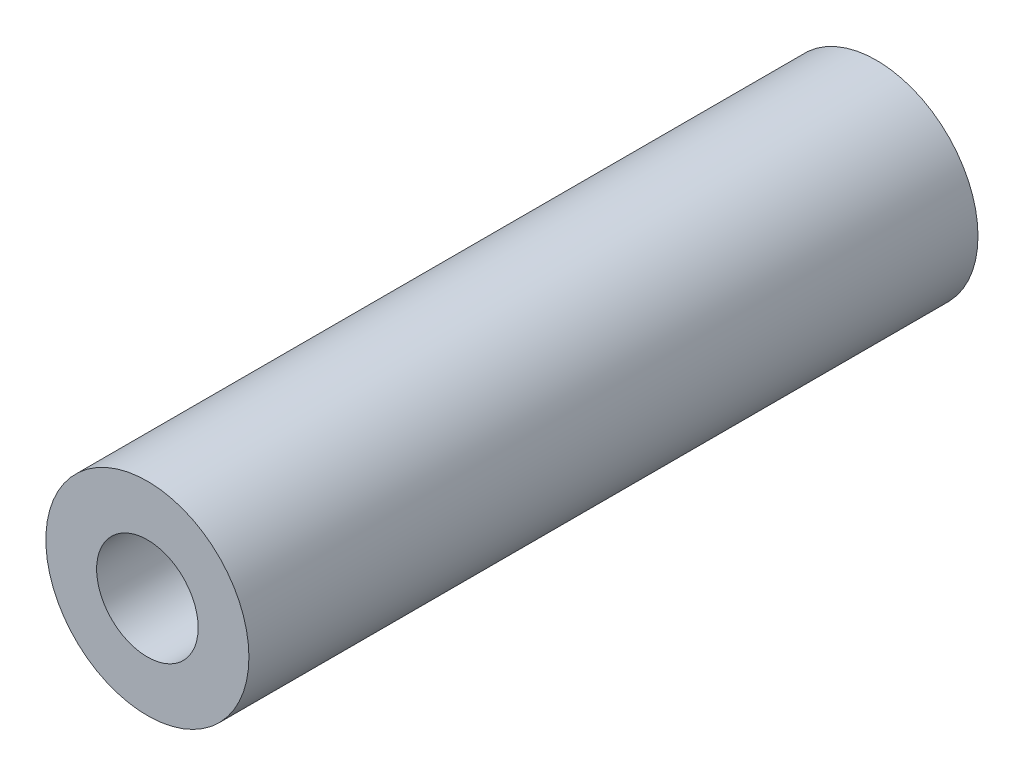
SolidWorks part; units mm, degrees
ref_plane "Front Plane" through (0, 0, 0) normal (0, 0, 1) x (1, 0, 0)
ref_plane "Top Plane" through (0, 0, 0) normal (0, 1, 0) x (1, 0, 0)
ref_plane "Right Plane" through (0, 0, 0) normal (1, 0, 0) x (0, 0, -1)
sketch "Sketch1" plane through (0, 0, 0) normal (0, 0, 1) x (1, 0, 0)
  circle A0 centre (0, 0) radius 5
  dimension "D1" = 10
extrude "Boss-Extrude1" add sketch "Sketch1" along normal blind 35.9
hole_wizard "Ø5.0mm Dowel Hole1" positions "Sketch2" profile "Sketch3" hole size "Ø5.0" standard "ANSI Metric" end condition up to next
sketch "Sketch2" plane through (0, 0, 35.9) normal (0, 0, 1) x (1, 0, 0)
  point P0 (0, 0)
sketch "Sketch3" plane through (0, 0, 35.9) normal (1, 0, 0) x (0, -1, 0)
  line L0 (0, 0) -> (0, 35.9)
  line L1 (0, 35.9) -> (2.5, 35.9)
  line L2 (2.5, 35.9) -> (2.5, 0)
  line L5 (2.5, 0) -> (0, 0)
  line L11 (0, -6.35) -> (0, 107.95) construction
  dimension "Thru Hole Dia." = 5
  dimension "Thru Hole Depth" = 35.9
